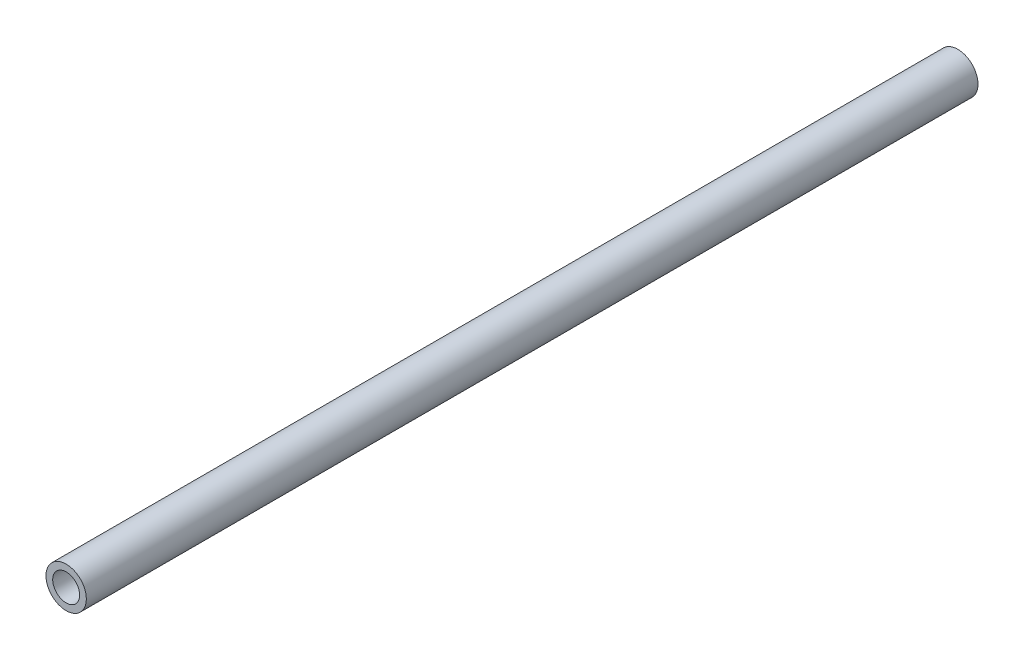
SolidWorks part; units mm, degrees
material "PVC Rigid"
ref_plane "Front Plane" through (0, 0, 0) normal (0, 0, 1) x (1, 0, 0)
ref_plane "Top Plane" through (0, 0, 0) normal (0, 1, 0) x (1, 0, 0)
ref_plane "Right Plane" through (0, 0, 0) normal (1, 0, 0) x (0, 0, -1)
sketch "Sketch1" plane through (0, 0, 0) normal (0, 0, 1) x (1, 0, 0)
  circle A0 centre (0, 0) radius 7.62
  circle A2 centre (0, 0) radius 5.08
  dimension "D1" = 15.24
  dimension "D2" = 10.16
extrude "Boss-Extrude1" add sketch "Sketch1" along normal blind 336.55
